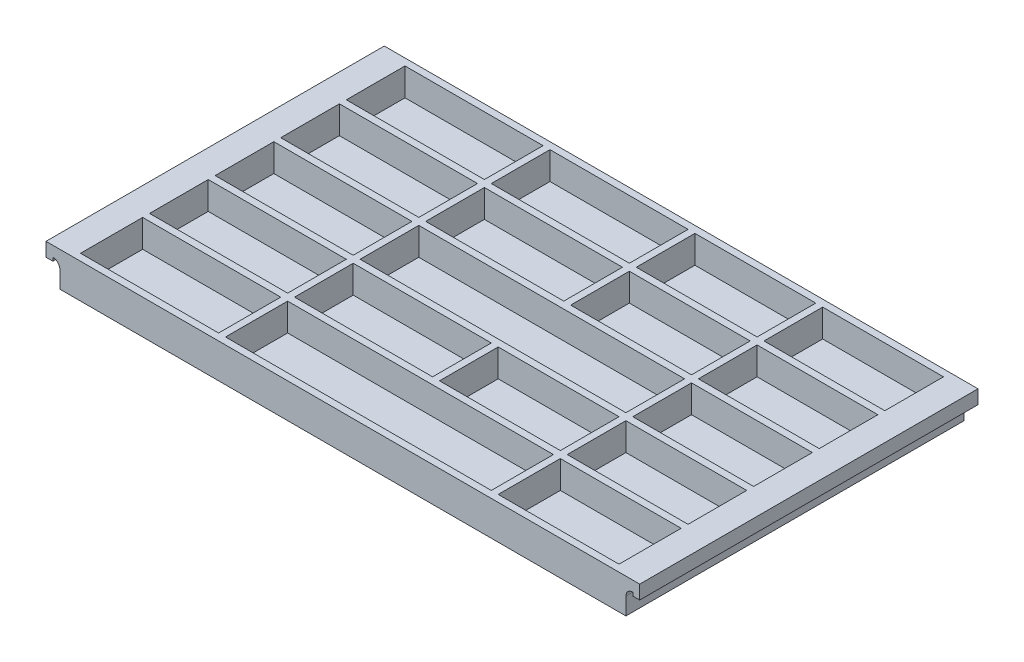
SolidWorks part; units mm, degrees
ref_plane "Front Plane" through (0, 0, 0) normal (0, 0, 1) x (1, 0, 0)
ref_plane "Top Plane" through (0, 0, 0) normal (0, 1, 0) x (1, 0, 0)
ref_plane "Right Plane" through (0, 0, 0) normal (1, 0, 0) x (0, 0, -1)
sketch "Sketch1" plane through (0, 0, 0) normal (0, 1, 0) x (1, 0, 0)
  line L1 (101.6, -62.23) -> (-101.6, -62.23)
  line L2 (101.6, -62.23) -> (101.6, 62.23)
  line L3 (101.6, 62.23) -> (-101.6, 62.23)
  line L4 (-101.6, -62.23) -> (-101.6, 62.23)
  line L5 (101.6, -62.23) -> (-101.6, 62.23) construction
  line L6 (101.6, 62.23) -> (-101.6, -62.23) construction
  line L32 (99.06, -59.69) -> (99.06, -36.83)
  line L37 (99.06, 59.69) -> (54.61, 59.69)
  line L39 (-99.06, -59.69) -> (-99.06, -36.83)
  line L41 (99.06, -59.69) -> (54.61, -59.69)
  line L42 (-48.26, 59.69) -> (-48.26, 38.1)
  line L45 (54.61, 59.69) -> (54.61, 38.1)
  line L46 (-99.06, 38.1) -> (-48.26, 38.1)
  line L51 (-99.06, 13.97) -> (-48.26, 13.97)
  line L53 (-44.4712, -27.2386) -> (-44.3417, -27.2342)
  line L54 (-99.06, -10.16) -> (-48.26, -10.16)
  line L55 (-99.06, -34.29) -> (-48.26, -34.29)
  line L56 (-45.72, 59.69) -> (-45.72, 38.1)
  line L57 (52.07, 59.69) -> (52.07, 38.1)
  line L60 (5.08, 59.69) -> (5.08, 38.1)
  line L61 (-99.06, 35.56) -> (-48.26, 35.56)
  line L62 (-99.06, 11.43) -> (-48.26, 11.43)
  line L63 (-99.06, -12.7) -> (-48.26, -12.7)
  line L64 (-99.06, -36.83) -> (-48.26, -36.83)
  line L66 (7.62, 59.69) -> (7.62, 38.1)
  line L69 (5.08, -12.7) -> (5.08, -34.29)
  line L70 (7.62, -12.7) -> (7.62, -34.29)
  line L71 (7.62, 35.56) -> (7.62, 13.97)
  line L73 (5.08, 35.56) -> (5.08, 13.97)
  line L76 (-48.26, 59.69) -> (-99.06, 59.69)
  line L78 (99.06, 59.69) -> (-99.06, 59.69) construction
  line L79 (-45.72, 35.56) -> (-45.72, 13.97)
  line L81 (-45.72, 59.69) -> (-45.72, -59.69) construction
  line L82 (-48.26, 35.56) -> (-48.26, 13.97)
  line L83 (5.08, 59.69) -> (-45.72, 59.69)
  line L84 (-48.26, 59.69) -> (-48.26, -59.69) construction
  line L85 (7.62, 38.1) -> (52.07, 38.1)
  line L86 (7.62, 35.56) -> (52.07, 35.56)
  line L87 (-99.06, 38.1) -> (99.06, 38.1) construction
  line L88 (-48.26, 11.43) -> (-48.26, -10.16)
  line L89 (-99.06, 35.56) -> (99.06, 35.56) construction
  line L90 (-45.72, 13.97) -> (5.08, 13.97)
  line L92 (-99.06, 13.97) -> (99.06, 13.97) construction
  line L93 (-45.72, 11.43) -> (-45.72, -10.16)
  line L94 (-45.72, 11.43) -> (52.07, 11.43)
  line L96 (-99.06, 11.43) -> (99.06, 11.43) construction
  line L97 (-99.06, 13.97) -> (-99.06, 35.56)
  line L99 (-99.06, -59.69) -> (-99.06, 59.69) construction
  line L100 (-99.06, 38.1) -> (-99.06, 59.69)
  line L101 (-99.06, -10.16) -> (-99.06, 11.43)
  line L102 (-45.72, -12.7) -> (-45.72, -34.29)
  line L103 (-45.72, -10.16) -> (52.07, -10.16)
  line L104 (-48.26, -12.7) -> (-48.26, -34.29)
  line L105 (-99.06, -10.16) -> (99.06, -10.16) construction
  line L106 (-45.72, -12.7) -> (5.08, -12.7)
  line L107 (-45.72, 35.56) -> (5.08, 35.56)
  line L108 (-99.06, -12.7) -> (99.06, -12.7) construction
  line L109 (-45.72, 38.1) -> (5.08, 38.1)
  line L110 (-45.72, -34.29) -> (5.08, -34.29)
  line L111 (-48.26, -36.83) -> (-48.26, -59.69)
  line L112 (-99.06, -34.29) -> (99.06, -34.29) construction
  line L113 (-45.72, -36.83) -> (-45.72, -59.69)
  line L114 (-45.72, -36.83) -> (52.07, -36.83)
  line L115 (-99.06, -34.29) -> (-99.06, -12.7)
  line L116 (-99.06, -36.83) -> (99.06, -36.83) construction
  line L117 (-48.26, -59.69) -> (-99.06, -59.69)
  line L118 (52.07, -59.69) -> (-45.72, -59.69)
  line L119 (99.06, -59.69) -> (-99.06, -59.69) construction
  line L120 (54.61, -36.83) -> (99.06, -36.83)
  line L121 (52.07, -36.83) -> (52.07, -59.69)
  line L122 (54.61, -36.83) -> (54.61, -59.69)
  line L123 (52.07, 59.69) -> (52.07, -59.69) construction
  line L124 (54.61, -34.29) -> (99.06, -34.29)
  line L125 (54.61, 59.69) -> (54.61, -59.69) construction
  line L126 (99.06, -34.29) -> (99.06, -12.7)
  line L127 (99.06, -10.16) -> (99.06, 11.43)
  line L128 (99.06, -59.69) -> (99.06, 59.69) construction
  line L129 (54.61, -12.7) -> (54.61, -34.29)
  line L130 (52.07, -12.7) -> (52.07, -34.29)
  line L131 (54.61, -10.16) -> (99.06, -10.16)
  line L132 (54.61, -12.7) -> (99.06, -12.7)
  line L133 (99.06, 13.97) -> (99.06, 35.56)
  line L134 (99.06, 38.1) -> (99.06, 59.69)
  line L135 (54.61, 35.56) -> (99.06, 35.56)
  line L136 (52.07, 35.56) -> (52.07, 13.97)
  line L137 (54.61, 35.56) -> (54.61, 13.97)
  line L138 (54.61, 38.1) -> (99.06, 38.1)
  line L139 (52.07, 59.69) -> (7.62, 59.69)
  line L140 (54.61, 13.97) -> (99.06, 13.97)
  line L141 (52.07, 11.43) -> (52.07, -10.16)
  line L142 (54.61, 11.43) -> (54.61, -10.16)
  line L143 (54.61, 11.43) -> (99.06, 11.43)
  line L144 (7.62, -12.7) -> (52.07, -12.7)
  line L145 (7.62, -34.29) -> (52.07, -34.29)
  line L146 (7.62, 13.97) -> (52.07, 13.97)
  point P0 (0, 0)
  point P6 (-109.855, 31.75)
  point P7 (109.855, 31.75)
  point P8 (-109.855, 1.27)
  point P9 (109.855, 1.27)
  point P10 (-109.855, -29.21)
  point P11 (109.855, -29.21)
  point P12 (-109.855, -26.67)
  point P13 (109.855, -26.67)
  point P14 (107.315, -59.69)
  point P15 (-107.315, -59.69)
  point P16 (-107.315, 59.69)
  point P17 (107.315, 59.69)
  point P18 (-109.855, 3.81)
  point P19 (109.855, 3.81)
  point P20 (-109.855, 34.29)
  point P21 (109.855, 34.29)
  point P74 (-66.675, 62.23)
  point P75 (-48.26, 34.29)
  point P80 (-64.135, 62.23)
  point P81 (-23.495, 62.23)
  point P86 (-23.495, 34.29)
  point P87 (19.685, 62.23)
  point P88 (19.685, 34.29)
  point P89 (62.865, 62.23)
  point P90 (54.61, 34.29)
  point P91 (-64.135, 34.29)
  point P92 (-20.955, 62.23)
  point P93 (-20.955, 34.29)
  point P94 (22.225, 62.23)
  point P95 (22.225, 34.29)
  point P96 (65.405, 62.23)
  point P97 (57.15, 38.1)
  dimension "D1" = 203.2
  dimension "D2" = 124.46
  dimension "D3" = 2.54
  dimension "D4" = 4
  dimension "D5" = 21.59
  dimension "D6" = 21.59
  dimension "D7" = 50.8
  dimension "D8" = 44.45
  dimension "D9" = 2.54
  dimension "D10" = 2.54
  dimension "D11" = 2.54
  dimension "D13" = 2.54
  dimension "D15" = 2.54
  dimension "D16" = 2.54
  dimension "D17" = 50.8
  dimension "D18" = 2.54
  dimension "D12" = 2.54
  dimension "D14" = 2.54
extrude "tray" add sketch "Sketch1" along normal blind 10.16 contours L4 L1 L2 L3 L146 L71 L86 L136 L145 L70 L144 L130 L140 L137 L135 L133 L139 L57 L85 L66 L138 L45 L37 L134 L122 L120 L32 L41 L110 L102 L106 L69 L109 L56 L83 L60 L51 L97 L61 L82 L46
sketch "Sketch3" plane through (0, 0, 0) normal (0, -1, 0) x (-1, 0, 0)
  line L1 (-101.6, 62.23) -> (101.6, 62.23)
  line L2 (-101.6, 62.23) -> (-101.6, -62.23)
  line L3 (-101.6, -62.23) -> (101.6, -62.23)
  line L4 (101.6, 62.23) -> (101.6, -62.23)
  line L5 (-101.6, 62.23) -> (101.6, -62.23) construction
  line L6 (-101.6, -62.23) -> (101.6, 62.23) construction
  point P0 (0, 0)
extrude "base" add sketch "Sketch3" along normal blind 2.54
sketch "Sketch4" plane through (0, 0, 62.23) normal (0, 0, 1) x (1, 0, 0)
  line L0 (-101.6, -2.54) -> (-101.6, 10.16)
  line L1 (-101.6, 10.16) -> (-109.22, 10.16)
  line L2 (-109.22, 10.16) -> (-109.22, 5.08)
  line L4 (-101.6, -2.54) -> (-104.14, -2.54)
  line L5 (-104.14, -2.54) -> (-104.14, 3.81)
  line L6 (0, 70.2947) -> (0, -83.8304) construction
  line L7 (-106.68, 6.35) -> (-106.68, 5.08)
  line L8 (-106.68, 5.08) -> (-109.22, 5.08)
  line L9 (101.6, -2.54) -> (104.14, -2.54)
  line L10 (104.14, -2.54) -> (104.14, 3.81)
  line L11 (101.6, 10.16) -> (109.22, 10.16)
  line L12 (101.6, -2.54) -> (101.6, 10.16)
  line L13 (109.22, 10.16) -> (109.22, 5.08)
  line L14 (106.68, 5.08) -> (109.22, 5.08)
  line L15 (106.68, 6.35) -> (106.68, 5.08)
  arc A1 (-106.68, 6.35) -> (-104.14, 3.81) centre (-106.68, 3.81) cw
  arc A2 (106.68, 6.35) -> (104.14, 3.81) centre (106.68, 3.81) ccw
  dimension "D1" = 5.08
  dimension "D3" = 2.54
  dimension "D2" = 2.54
  dimension "D4" = 7.62
  dimension "D5" = 1.27
extrude "handle" add sketch "Sketch4" against normal up to surface (124.46 mm away) contours L2 L8 L7 A1 L5 L4 L0 L1 | L9 L10 A2 L15 L14 L13 L11 L12 up to face at (0, 3.81, -62.23)
